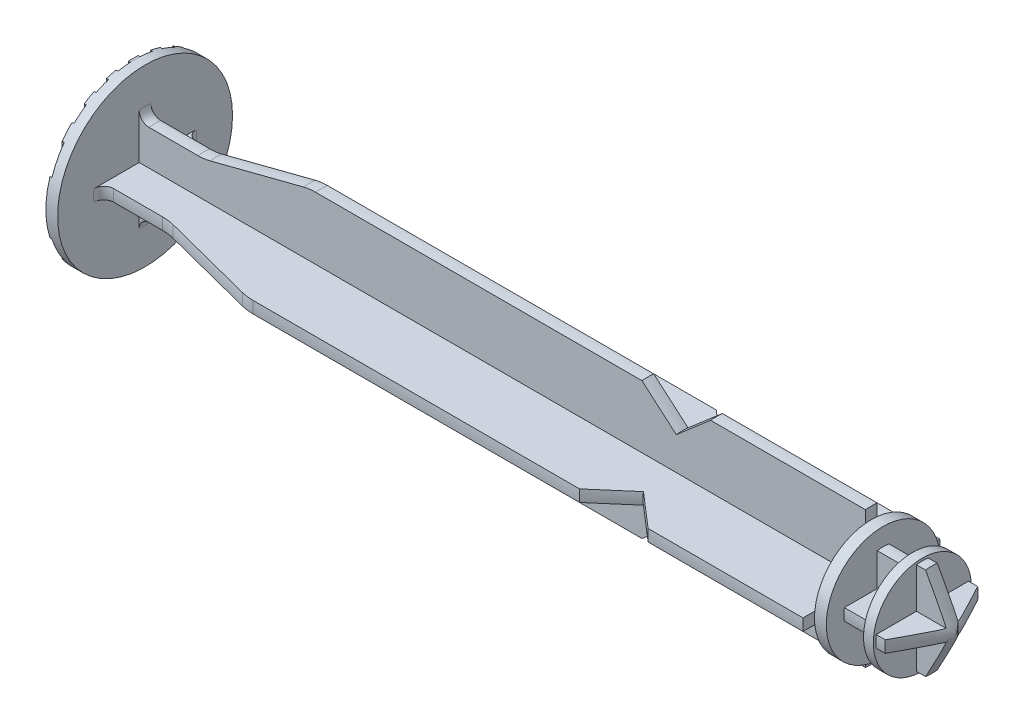
SolidWorks part; units mm, degrees
material "Polyethylene Cross-Linked"
ref_plane "Front Plane" through (0, 0, 0) normal (0, 0, 1) x (1, 0, 0)
ref_plane "Top Plane" through (0, 0, 0) normal (0, 1, 0) x (1, 0, 0)
ref_plane "Right Plane" through (0, 0, 0) normal (1, 0, 0) x (0, 0, -1)
sketch "Sketch1" plane through (0, 0, 0) normal (0, 0, 1) x (1, 0, 0)
  line L0 (84, 0) -> (-84, 0) construction
  line L1 (0, 0) -> (0, 8.925)
  line L2 (0, 8.925) -> (1.2, 8.925)
  line L3 (1.2, 8.925) -> (1.2, 5.25)
  line L4 (2.2, 4.25) -> (7.2, 4.25)
  line L5 (8.4402, 4.4063) -> (17.9598, 6.8437)
  line L6 (19.2, 7) -> (52.5, 7)
  line L7 (52.5, 7) -> (56, 4)
  line L8 (56, 4) -> (59.5, 7)
  line L9 (59.5, 7) -> (75.3, 7)
  line L10 (75.3, 7) -> (75.3, 5.8)
  line L11 (75.3, 5.8) -> (76.5, 5.8)
  line L12 (76.5, 5.8) -> (76.5, 4)
  line L13 (76.5, 4) -> (79.5, 4)
  line L14 (79.5, 4) -> (79.5, 5)
  line L15 (79.5, 5) -> (81.3, 5)
  line L16 (81.3, 5) -> (84, 0)
  line L17 (0, 0) -> (84, 0)
  arc A0 (1.2, 5.25) -> (2.2, 4.25) centre (2.2, 5.25) ccw
  arc A1 (17.9598, 6.8437) -> (19.2, 7) centre (19.2, 2) cw
  arc A2 (7.2, 4.25) -> (8.4402, 4.4063) centre (7.2, 9.25) ccw
  point P4 (0, 0)
  dimension "D14" = 1
  dimension "D15" = 5
  dimension "D1" = 1.2
  dimension "D2" = 7.5
  dimension "D3" = 17.85
  dimension "D4" = 8.5
  dimension "D5" = 84
  dimension "D6" = 7
  dimension "D7" = 7
  dimension "D8" = 14
  dimension "D9" = 11.6
  dimension "D10" = 8
  dimension "D11" = 10
  dimension "D12" = 28
  dimension "D13" = 4.5
  dimension "D16" = 6
  dimension "D17" = 18
  dimension "D18" = 2.7
  dimension "D19" = 118.369
revolve "Revolve1" add sketch "Sketch1" angle 360 about L0
sketch "Sketch2" plane through (1.2, 0, 0) normal (1, 0, 0) x (0, 0, -1)
  line L0 (17.7295, 0) -> (-17.7295, 0) construction
  line L1 (0, -17.5817) -> (0, 17.5817) construction
  line L2 (-0.6, 8.9048) -> (-0.6, 0.6)
  line L3 (-0.6, 0.6) -> (-8.9048, 0.6)
  line L4 (0.6, 0.6) -> (0.6, 8.9048)
  line L5 (8.9048, 0.6) -> (0.6, 0.6)
  line L6 (0.6, -0.6) -> (8.9048, -0.6)
  line L7 (0.6, -8.9048) -> (0.6, -0.6)
  line L8 (-0.6, -0.6) -> (-0.6, -8.9048)
  line L9 (-8.9048, -0.6) -> (-0.6, -0.6)
  circle A0 centre (0, 0) radius 8.925 construction
  arc A1 (-8.9048, 0.6) -> (-8.9048, -0.6) centre (0, 0) ccw
  arc A2 (0.6, 8.9048) -> (-0.6, 8.9048) centre (0, 0) ccw
  arc A3 (8.9048, -0.6) -> (8.9048, 0.6) centre (0, 0) ccw
  arc A4 (-0.6, -8.9048) -> (0.6, -8.9048) centre (0, 0) ccw
  point P5 (0, 0)
  point P9 (0, 0)
  point P27 (0, 0)
  dimension "D3" = 1.2
  dimension "D2" = 4
extrude "Cut-Extrude1" cut sketch "Sketch2" along normal up to surface (74.1 mm away) flip side to cut up to face at (75.3, 0, -7)
sketch "Sketch3" plane through (0, 0, 0) normal (-1, 0, 0) x (0, 0, 1)
  line L0 (2.75, -8.911) -> (1.75, -8.911)
  line L1 (0.5, -8.911) -> (-0.5, -8.911)
  line L2 (0.5, -8.911) -> (0.5, 8.911)
  line L3 (0.5, 8.911) -> (-0.5, 8.911)
  line L4 (-0.5, -8.911) -> (-0.5, 8.911)
  line L5 (0.5, -8.911) -> (-0.5, 8.911) construction
  line L6 (0.5, 8.911) -> (-0.5, -8.911) construction
  line L7 (1.75, -8.911) -> (1.75, 8.911)
  line L8 (2.75, 8.911) -> (1.75, 8.911)
  line L9 (2.75, -8.911) -> (2.75, 8.911)
  line L10 (5, -8.911) -> (4, -8.911)
  line L11 (4, -8.911) -> (4, 8.911)
  line L12 (5, 8.911) -> (4, 8.911)
  line L13 (5, -8.911) -> (5, 8.911)
  line L14 (7.25, -8.911) -> (6.25, -8.911)
  line L15 (6.25, -8.911) -> (6.25, 8.911)
  line L16 (7.25, 8.911) -> (6.25, 8.911)
  line L17 (7.25, -8.911) -> (7.25, 8.911)
  line L18 (9.5, -8.911) -> (8.5, -8.911)
  line L19 (8.5, -8.911) -> (8.5, 8.911)
  line L20 (9.5, 8.911) -> (8.5, 8.911)
  line L21 (9.5, -8.911) -> (9.5, 8.911)
  line L22 (11.75, -8.911) -> (10.75, -8.911)
  line L23 (10.75, -8.911) -> (10.75, 8.911)
  line L24 (11.75, 8.911) -> (10.75, 8.911)
  line L25 (11.75, -8.911) -> (11.75, 8.911)
  line L26 (14, -8.911) -> (13, -8.911)
  line L27 (13, -8.911) -> (13, 8.911)
  line L28 (14, 8.911) -> (13, 8.911)
  line L29 (14, -8.911) -> (14, 8.911)
  line L30 (-1.75, -8.911) -> (-2.75, -8.911)
  line L31 (-2.75, -8.911) -> (-2.75, 8.911)
  line L32 (-1.75, 8.911) -> (-2.75, 8.911)
  line L33 (-1.75, -8.911) -> (-1.75, 8.911)
  line L34 (-4, -8.911) -> (-5, -8.911)
  line L35 (-5, -8.911) -> (-5, 8.911)
  line L36 (-4, 8.911) -> (-5, 8.911)
  line L37 (-4, -8.911) -> (-4, 8.911)
  line L38 (-6.25, -8.911) -> (-7.25, -8.911)
  line L39 (-7.25, -8.911) -> (-7.25, 8.911)
  line L40 (-6.25, 8.911) -> (-7.25, 8.911)
  line L41 (-6.25, -8.911) -> (-6.25, 8.911)
  line L42 (-8.5, -8.911) -> (-9.5, -8.911)
  line L43 (-9.5, -8.911) -> (-9.5, 8.911)
  line L44 (-8.5, 8.911) -> (-9.5, 8.911)
  line L45 (-8.5, -8.911) -> (-8.5, 8.911)
  line L46 (-10.75, -8.911) -> (-11.75, -8.911)
  line L47 (-11.75, -8.911) -> (-11.75, 8.911)
  line L48 (-10.75, 8.911) -> (-11.75, 8.911)
  line L49 (-10.75, -8.911) -> (-10.75, 8.911)
  line L50 (-13, -8.911) -> (-14, -8.911)
  line L51 (-14, -8.911) -> (-14, 8.911)
  line L52 (-13, 8.911) -> (-14, 8.911)
  line L53 (-13, -8.911) -> (-13, 8.911)
  circle A0 centre (0, 0) radius 8.925 construction
  point P0 (0, 0)
  dimension "D1" = 1
  dimension "D3" = 2.25
  dimension "D2" = 7
  dimension "D4" = 7
extrude "Cut-Extrude2" cut sketch "Sketch3" against normal blind 0.2 flip side to cut
sketch "Sketch4" plane through (76.5, 0, 0) normal (1, 0, 0) x (0, 0, -1)
  line L8 (0.6, 0.6) -> (0.6, 8.9048)
  line L9 (-0.6, 8.9048) -> (-0.6, 0.6)
  line L10 (-0.6, 0.6) -> (-8.9048, 0.6)
  line L11 (-8.9048, -0.6) -> (-0.6, -0.6)
  line L12 (-0.6, -0.6) -> (-0.6, -8.9048)
  line L13 (0.6, -8.9048) -> (0.6, -0.6)
  line L14 (0.6, -0.6) -> (8.9048, -0.6)
  line L15 (8.9048, 0.6) -> (0.6, 0.6)
  line L16 (0.6, 0.6) -> (0.6, 8.9048)
  line L17 (-0.6, 8.9048) -> (-0.6, 0.6)
  line L18 (-0.6, 0.6) -> (-8.9048, 0.6)
  line L19 (-8.9048, -0.6) -> (-0.6, -0.6)
  line L20 (-0.6, -0.6) -> (-0.6, -8.9048)
  line L21 (0.6, -8.9048) -> (0.6, -0.6)
  line L22 (0.6, -0.6) -> (8.9048, -0.6)
  line L23 (8.9048, 0.6) -> (0.6, 0.6)
  arc A4 (0.6, 8.9048) -> (-0.6, 8.9048) centre (0, 0) ccw
  arc A5 (-8.9048, 0.6) -> (-8.9048, -0.6) centre (0, 0) ccw
  arc A6 (-0.6, -8.9048) -> (0.6, -8.9048) centre (0, 0) ccw
  arc A7 (8.9048, -0.6) -> (8.9048, 0.6) centre (0, 0) ccw
  arc A8 (0.6, 8.9048) -> (-0.6, 8.9048) centre (0, 0) ccw
  arc A9 (-8.9048, 0.6) -> (-8.9048, -0.6) centre (0, 0) ccw
  arc A10 (-0.6, -8.9048) -> (0.6, -8.9048) centre (0, 0) ccw
  arc A11 (8.9048, -0.6) -> (8.9048, 0.6) centre (0, 0) ccw
  dimension "D1" = 0
extrude "Cut-Extrude3" cut sketch "Sketch4" along normal up to surface (3 mm away) flip side to cut up to face at (79.5, 0, -4)
ref_plane "Plane1" through (84, 0, 0) normal (1, 0, 0) x (0, 0, -1)
sketch "Sketch5" plane through (84, 0, 0) normal (1, 0, 0) x (0, 0, -1)
  line L8 (0.6, 0.6) -> (0.6, 8.9048)
  line L9 (-0.6, 8.9048) -> (-0.6, 0.6)
  line L10 (-0.6, 0.6) -> (-8.9048, 0.6)
  line L11 (-8.9048, -0.6) -> (-0.6, -0.6)
  line L12 (-0.6, -0.6) -> (-0.6, -8.9048)
  line L13 (0.6, -8.9048) -> (0.6, -0.6)
  line L14 (0.6, -0.6) -> (8.9048, -0.6)
  line L15 (8.9048, 0.6) -> (0.6, 0.6)
  line L16 (0.6, 0.6) -> (0.6, 4.712)
  line L17 (-0.6, 4.712) -> (-0.6, 0.6)
  line L18 (-0.6, 0.6) -> (-4.712, 0.6)
  line L19 (-4.712, -0.6) -> (-0.6, -0.6)
  line L20 (-0.6, -0.6) -> (-0.6, -4.712)
  line L21 (0.6, -4.712) -> (0.6, -0.6)
  line L22 (0.6, -0.6) -> (4.712, -0.6)
  line L23 (4.712, 0.6) -> (0.6, 0.6)
  arc A0 (-4.712, 0.6) -> (-4.712, -0.6) centre (0, 0) ccw
  arc A1 (4.712, -0.6) -> (4.712, 0.6) centre (0, 0) ccw
  arc A2 (0.6, 4.712) -> (-0.6, 4.712) centre (0, 0) ccw
  arc A3 (-0.6, -4.712) -> (0.6, -4.712) centre (0, 0) ccw
  arc A4 (0.6, 8.9048) -> (-0.6, 8.9048) centre (0, 0) ccw
  arc A5 (-8.9048, 0.6) -> (-8.9048, -0.6) centre (0, 0) ccw
  arc A6 (-0.6, -8.9048) -> (0.6, -8.9048) centre (0, 0) ccw
  arc A7 (8.9048, -0.6) -> (8.9048, 0.6) centre (0, 0) ccw
  dimension "D2" = 9.5
  dimension "D1" = 0
extrude "Cut-Extrude4" cut sketch "Sketch5" against normal blind 3.5 flip side to cut
